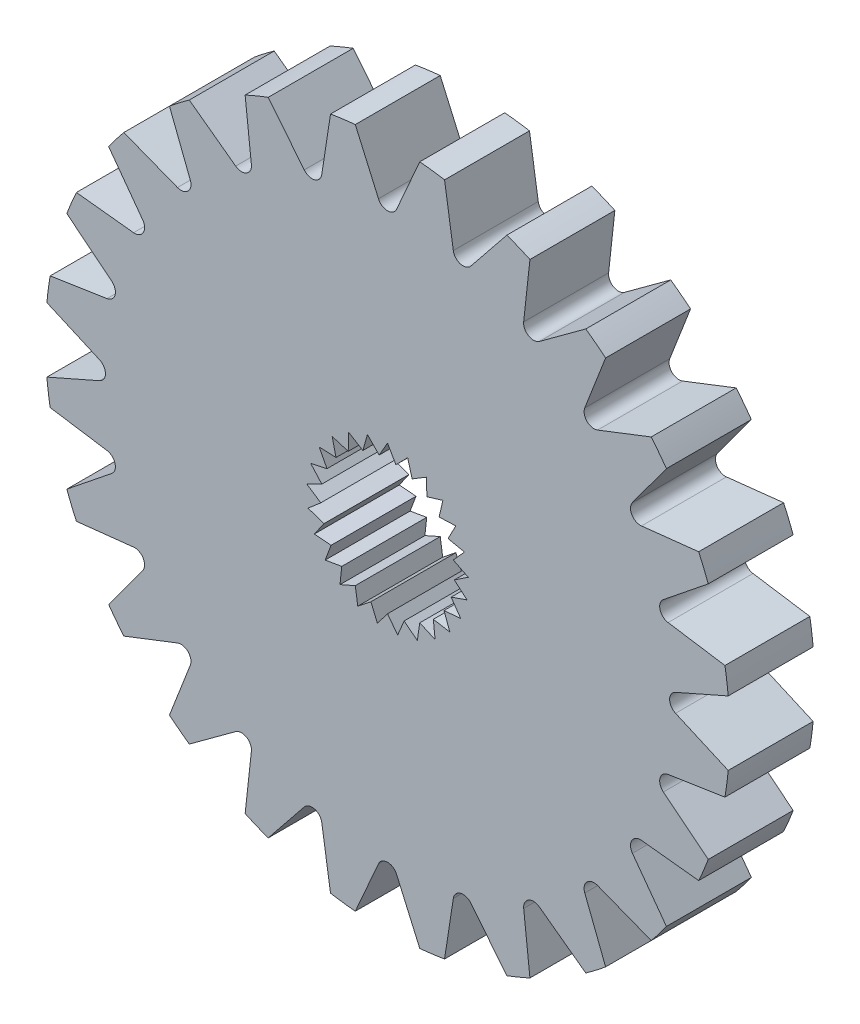
SolidWorks part; units mm, degrees
ref_plane "Front Plane" through (0, 0, 0) normal (0, 0, 1) x (1, 0, 0)
ref_plane "Top Plane" through (0, 0, 0) normal (0, 1, 0) x (1, 0, 0)
ref_plane "Right Plane" through (0, 0, 0) normal (1, 0, 0) x (0, 0, -1)
sketch "Sketch1" plane through (0, 0, 0) normal (0, 0, 1) x (1, 0, 0)
  line L0 (0, 3.048) -> (0, 0) construction
  line L1 (0, 3.048) -> (-0.3159, 2.5008)
  line L2 (0, 3.048) -> (0.3159, 2.5008)
  line L3 (-0.3159, 2.5008) -> (0.3159, 2.5008) construction
  line L4 (0.758, 2.9522) -> (0.3159, 2.5008)
  line L5 (0.758, 2.9522) -> (0.9279, 2.3437)
  line L6 (0.3159, 2.5008) -> (0.9279, 2.3437) construction
  line L7 (1.4684, 2.671) -> (0.9279, 2.3437)
  line L8 (1.4684, 2.671) -> (1.4816, 2.0393)
  line L9 (0.9279, 2.3437) -> (1.4816, 2.0393) construction
  line L10 (2.0865, 2.2219) -> (1.4816, 2.0393)
  line L11 (2.0865, 2.2219) -> (1.9422, 1.6067)
  line L12 (1.4816, 2.0393) -> (1.9422, 1.6067) construction
  line L13 (2.5735, 1.6332) -> (1.9422, 1.6067)
  line L14 (2.5735, 1.6332) -> (2.2808, 1.0733)
  line L15 (1.9422, 1.6067) -> (2.2808, 1.0733) construction
  line L16 (2.8988, 0.9419) -> (2.2808, 1.0733)
  line L17 (2.8988, 0.9419) -> (2.476, 0.4723)
  line L18 (2.2808, 1.0733) -> (2.476, 0.4723) construction
  line L19 (3.042, 0.1914) -> (2.476, 0.4723)
  line L20 (3.042, 0.1914) -> (2.5157, -0.1583)
  line L21 (2.476, 0.4723) -> (2.5157, -0.1583) construction
  line L22 (2.994, -0.5711) -> (2.5157, -0.1583)
  line L23 (2.994, -0.5711) -> (2.3973, -0.7789)
  line L24 (2.5157, -0.1583) -> (2.3973, -0.7789) construction
  line L25 (2.7579, -1.2978) -> (2.3973, -0.7789)
  line L26 (2.7579, -1.2978) -> (2.1283, -1.3506)
  line L27 (2.3973, -0.7789) -> (2.1283, -1.3506) construction
  line L28 (2.3485, -1.9429) -> (2.1283, -1.3506)
  line L29 (2.3485, -1.9429) -> (1.7255, -1.8375)
  line L30 (2.1283, -1.3506) -> (1.7255, -1.8375) construction
  line L31 (1.7916, -2.4659) -> (1.7255, -1.8375)
  line L32 (1.7916, -2.4659) -> (1.2143, -2.2089)
  line L33 (1.7255, -1.8375) -> (1.2143, -2.2089) construction
  line L34 (1.122, -2.834) -> (1.2143, -2.2089)
  line L35 (1.122, -2.834) -> (0.6269, -2.4415)
  line L36 (1.2143, -2.2089) -> (0.6269, -2.4415) construction
  line L37 (0.382, -3.024) -> (0.6269, -2.4415)
  line L38 (0.382, -3.024) -> (0, -2.5207)
  line L39 (0.6269, -2.4415) -> (0, -2.5207) construction
  line L40 (-0.382, -3.024) -> (0, -2.5207)
  line L41 (-0.382, -3.024) -> (-0.6269, -2.4415)
  line L42 (0, -2.5207) -> (-0.6269, -2.4415) construction
  line L43 (-1.122, -2.834) -> (-0.6269, -2.4415)
  line L44 (-1.122, -2.834) -> (-1.2143, -2.2089)
  line L45 (-0.6269, -2.4415) -> (-1.2143, -2.2089) construction
  line L46 (-1.7916, -2.4659) -> (-1.2143, -2.2089)
  line L47 (-1.7916, -2.4659) -> (-1.7255, -1.8375)
  line L48 (-1.2143, -2.2089) -> (-1.7255, -1.8375) construction
  line L49 (-2.3485, -1.9429) -> (-1.7255, -1.8375)
  line L50 (-2.3485, -1.9429) -> (-2.1283, -1.3506)
  line L51 (-1.7255, -1.8375) -> (-2.1283, -1.3506) construction
  line L52 (-2.7579, -1.2978) -> (-2.1283, -1.3506)
  line L53 (-2.7579, -1.2978) -> (-2.3973, -0.7789)
  line L54 (-2.1283, -1.3506) -> (-2.3973, -0.7789) construction
  line L55 (-2.994, -0.5711) -> (-2.3973, -0.7789)
  line L56 (-2.994, -0.5711) -> (-2.5157, -0.1583)
  line L57 (-2.3973, -0.7789) -> (-2.5157, -0.1583) construction
  line L58 (-3.042, 0.1914) -> (-2.5157, -0.1583)
  line L59 (-3.042, 0.1914) -> (-2.476, 0.4723)
  line L60 (-2.5157, -0.1583) -> (-2.476, 0.4723) construction
  line L61 (-2.8988, 0.9419) -> (-2.476, 0.4723)
  line L62 (-2.8988, 0.9419) -> (-2.2808, 1.0733)
  line L63 (-2.476, 0.4723) -> (-2.2808, 1.0733) construction
  line L64 (-2.5735, 1.6332) -> (-2.2808, 1.0733)
  line L65 (-2.5735, 1.6332) -> (-1.9422, 1.6067)
  line L66 (-2.2808, 1.0733) -> (-1.9422, 1.6067) construction
  line L67 (-2.0865, 2.2219) -> (-1.9422, 1.6067)
  line L68 (-2.0865, 2.2219) -> (-1.4816, 2.0393)
  line L69 (-1.9422, 1.6067) -> (-1.4816, 2.0393) construction
  line L70 (-1.4684, 2.671) -> (-1.4816, 2.0393)
  line L71 (-1.4684, 2.671) -> (-0.9279, 2.3437)
  line L72 (-1.4816, 2.0393) -> (-0.9279, 2.3437) construction
  line L73 (-0.758, 2.9522) -> (-0.9279, 2.3437)
  line L74 (-0.758, 2.9522) -> (-0.3159, 2.5008)
  line L75 (-0.9279, 2.3437) -> (-0.3159, 2.5008) construction
  circle A1 centre (0, 0) radius 12.8934
  point P0 (0, 2.5008)
  point P12 (0.6219, 2.4222)
  point P16 (1.2048, 2.1915)
  point P20 (1.7119, 1.823)
  point P24 (2.1115, 1.34)
  point P28 (2.3784, 0.7728)
  point P32 (2.4959, 0.157)
  point P36 (2.4565, -0.4686)
  point P40 (2.2628, -1.0648)
  point P44 (1.9269, -1.5941)
  point P48 (1.4699, -2.0232)
  point P52 (0.9206, -2.3252)
  point P56 (0.3134, -2.4811)
  point P60 (-0.3134, -2.4811)
  point P64 (-0.9206, -2.3252)
  point P68 (-1.4699, -2.0232)
  point P72 (-1.9269, -1.5941)
  point P76 (-2.2628, -1.0648)
  point P80 (-2.4565, -0.4686)
  point P84 (-2.4959, 0.157)
  point P88 (-2.3784, 0.7728)
  point P92 (-2.1115, 1.34)
  point P96 (-1.7119, 1.823)
  point P100 (-1.2048, 2.1915)
  point P104 (-0.6219, 2.4222)
  dimension "D1" = 25
  dimension "D3" = 25.7868
  dimension "D2" = 60
extrude "Boss-Extrude1" add sketch "Sketch1" along normal blind 3.2004
sketch "Sketch2" plane through (0, 0, 3.2004) normal (0, 0, 1) x (1, 0, 0)
  line L0 (-1.2151, 12.836) -> (1.2151, 12.836) construction
  line L1 (-1.2151, 12.836) -> (-0.3419, 10.8524)
  line L2 (0, 0) -> (0.8437, 12.836) construction
  line L3 (0.3419, 10.8524) -> (1.2151, 12.836)
  line L4 (-0.3419, 10.8524) -> (0.3419, 10.8524) construction
  line L5 (3.1391, 10.3941) -> (4.4959, 12.0841)
  line L6 (-0.7785, 11.8442) -> (0.7785, 11.8442) construction
  line L7 (2.1485, 12.7131) -> (2.4786, 10.5711)
  line L8 (5.7223, 9.2275) -> (7.4703, 10.5087)
  line L9 (5.3657, 11.7239) -> (5.1301, 9.5694)
  line L10 (7.9156, 7.4321) -> (9.9357, 8.2172)
  line L11 (8.2172, 9.9357) -> (7.4321, 7.9156)
  line L12 (9.5694, 5.1301) -> (11.7239, 5.3657)
  line L13 (10.5087, 7.4703) -> (9.2275, 5.7223)
  line L14 (10.5711, 2.4786) -> (12.7131, 2.1485)
  line L15 (12.0841, 4.4959) -> (10.3941, 3.1391)
  line L16 (10.8524, -0.3419) -> (12.836, -1.2151)
  line L17 (12.836, 1.2151) -> (10.8524, 0.3419)
  line L18 (10.3941, -3.1391) -> (12.0841, -4.4959)
  line L19 (12.7131, -2.1485) -> (10.5711, -2.4786)
  line L20 (9.2275, -5.7223) -> (10.5087, -7.4703)
  line L21 (11.7239, -5.3657) -> (9.5694, -5.1301)
  line L22 (7.4321, -7.9156) -> (8.2172, -9.9357)
  line L23 (9.9357, -8.2172) -> (7.9156, -7.4321)
  line L24 (5.1301, -9.5694) -> (5.3657, -11.7239)
  line L25 (7.4703, -10.5087) -> (5.7223, -9.2275)
  line L26 (2.4786, -10.5711) -> (2.1485, -12.7131)
  line L27 (4.4959, -12.0841) -> (3.1391, -10.3941)
  line L28 (-0.3419, -10.8524) -> (-1.2151, -12.836)
  line L29 (1.2151, -12.836) -> (0.3419, -10.8524)
  line L30 (-3.1391, -10.3941) -> (-4.4959, -12.0841)
  line L31 (-2.1485, -12.7131) -> (-2.4786, -10.5711)
  line L32 (-5.7223, -9.2275) -> (-7.4703, -10.5087)
  line L33 (-5.3657, -11.7239) -> (-5.1301, -9.5694)
  line L34 (-7.9156, -7.4321) -> (-9.9357, -8.2172)
  line L35 (-8.2172, -9.9357) -> (-7.4321, -7.9156)
  line L36 (-9.5694, -5.1301) -> (-11.7239, -5.3657)
  line L37 (-10.5087, -7.4703) -> (-9.2275, -5.7223)
  line L38 (-10.5711, -2.4786) -> (-12.7131, -2.1485)
  line L39 (-12.0841, -4.4959) -> (-10.3941, -3.1391)
  line L40 (-10.8524, 0.3419) -> (-12.836, 1.2151)
  line L41 (-12.836, -1.2151) -> (-10.8524, -0.3419)
  line L42 (-10.3941, 3.1391) -> (-12.0841, 4.4959)
  line L43 (-12.7131, 2.1485) -> (-10.5711, 2.4786)
  line L44 (-9.2275, 5.7223) -> (-10.5087, 7.4703)
  line L45 (-11.7239, 5.3657) -> (-9.5694, 5.1301)
  line L46 (-7.4321, 7.9156) -> (-8.2172, 9.9357)
  line L47 (-9.9357, 8.2172) -> (-7.9156, 7.4321)
  line L48 (-5.1301, 9.5694) -> (-5.3657, 11.7239)
  line L49 (-7.4703, 10.5087) -> (-5.7223, 9.2275)
  line L50 (-2.4786, 10.5711) -> (-2.1485, 12.7131)
  line L51 (-4.4959, 12.0841) -> (-3.1391, 10.3941)
  line L180 (0, 12.836) -> (0, 0) construction
  arc A0 (0.3419, 10.8524) -> (-0.3419, 10.8524) centre (0, 11.0029) cw
  arc A1 (1.2151, 12.836) -> (-1.2151, 12.836) centre (0, 0) ccw
  arc A2 (4.4959, 12.0841) -> (2.1485, 12.7131) centre (0, 0) ccw
  circle A3 centre (0, 0) radius 12.8934 construction
  arc A4 (3.1391, 10.3941) -> (2.4786, 10.5711) centre (2.8478, 10.628) cw
  arc A5 (7.4703, 10.5087) -> (5.3657, 11.7239) centre (0, 0) ccw
  arc A6 (5.7223, 9.2275) -> (5.1301, 9.5694) centre (5.5015, 9.5288) cw
  arc A7 (9.9357, 8.2172) -> (8.2172, 9.9357) centre (0, 0) ccw
  arc A8 (7.9156, 7.4321) -> (7.4321, 7.9156) centre (7.7802, 7.7802) cw
  arc A9 (11.7239, 5.3657) -> (10.5087, 7.4703) centre (0, 0) ccw
  arc A10 (9.5694, 5.1301) -> (9.2275, 5.7223) centre (9.5288, 5.5015) cw
  arc A11 (12.7131, 2.1485) -> (12.0841, 4.4959) centre (0, 0) ccw
  arc A12 (10.5711, 2.4786) -> (10.3941, 3.1391) centre (10.628, 2.8478) cw
  arc A13 (12.836, -1.2151) -> (12.836, 1.2151) centre (0, 0) ccw
  arc A14 (10.8524, -0.3419) -> (10.8524, 0.3419) centre (11.0029, 0) cw
  arc A15 (12.0841, -4.4959) -> (12.7131, -2.1485) centre (0, 0) ccw
  arc A16 (10.3941, -3.1391) -> (10.5711, -2.4786) centre (10.628, -2.8478) cw
  arc A17 (10.5087, -7.4703) -> (11.7239, -5.3657) centre (0, 0) ccw
  arc A18 (9.2275, -5.7223) -> (9.5694, -5.1301) centre (9.5288, -5.5015) cw
  arc A19 (8.2172, -9.9357) -> (9.9357, -8.2172) centre (0, 0) ccw
  arc A20 (7.4321, -7.9156) -> (7.9156, -7.4321) centre (7.7802, -7.7802) cw
  arc A21 (5.3657, -11.7239) -> (7.4703, -10.5087) centre (0, 0) ccw
  arc A22 (5.1301, -9.5694) -> (5.7223, -9.2275) centre (5.5015, -9.5288) cw
  arc A23 (2.1485, -12.7131) -> (4.4959, -12.0841) centre (0, 0) ccw
  arc A24 (2.4786, -10.5711) -> (3.1391, -10.3941) centre (2.8478, -10.628) cw
  arc A25 (-1.2151, -12.836) -> (1.2151, -12.836) centre (0, 0) ccw
  arc A26 (-0.3419, -10.8524) -> (0.3419, -10.8524) centre (0, -11.0029) cw
  arc A27 (-4.4959, -12.0841) -> (-2.1485, -12.7131) centre (0, 0) ccw
  arc A28 (-3.1391, -10.3941) -> (-2.4786, -10.5711) centre (-2.8478, -10.628) cw
  arc A29 (-7.4703, -10.5087) -> (-5.3657, -11.7239) centre (0, 0) ccw
  arc A30 (-5.7223, -9.2275) -> (-5.1301, -9.5694) centre (-5.5015, -9.5288) cw
  arc A31 (-9.9357, -8.2172) -> (-8.2172, -9.9357) centre (0, 0) ccw
  arc A32 (-7.9156, -7.4321) -> (-7.4321, -7.9156) centre (-7.7802, -7.7802) cw
  arc A33 (-11.7239, -5.3657) -> (-10.5087, -7.4703) centre (0, 0) ccw
  arc A34 (-9.5694, -5.1301) -> (-9.2275, -5.7223) centre (-9.5288, -5.5015) cw
  arc A35 (-12.7131, -2.1485) -> (-12.0841, -4.4959) centre (0, 0) ccw
  arc A36 (-10.5711, -2.4786) -> (-10.3941, -3.1391) centre (-10.628, -2.8478) cw
  arc A37 (-12.836, 1.2151) -> (-12.836, -1.2151) centre (0, 0) ccw
  arc A38 (-10.8524, 0.3419) -> (-10.8524, -0.3419) centre (-11.0029, 0) cw
  arc A39 (-12.0841, 4.4959) -> (-12.7131, 2.1485) centre (0, 0) ccw
  arc A40 (-10.3941, 3.1391) -> (-10.5711, 2.4786) centre (-10.628, 2.8478) cw
  arc A41 (-10.5087, 7.4703) -> (-11.7239, 5.3657) centre (0, 0) ccw
  arc A42 (-9.2275, 5.7223) -> (-9.5694, 5.1301) centre (-9.5288, 5.5015) cw
  arc A43 (-8.2172, 9.9357) -> (-9.9357, 8.2172) centre (0, 0) ccw
  arc A44 (-7.4321, 7.9156) -> (-7.9156, 7.4321) centre (-7.7802, 7.7802) cw
  arc A45 (-5.3657, 11.7239) -> (-7.4703, 10.5087) centre (0, 0) ccw
  arc A46 (-5.1301, 9.5694) -> (-5.7223, 9.2275) centre (-5.5015, 9.5288) cw
  arc A47 (-2.1485, 12.7131) -> (-4.4959, 12.0841) centre (0, 0) ccw
  arc A48 (-2.4786, 10.5711) -> (-3.1391, 10.3941) centre (-2.8478, 10.628) cw
  point P1 (0, 11.8442)
  point P132 (0, 0)
  point P212 (0, 0)
  dimension "D1" = 0.9918
  dimension "D2" = 20
  dimension "D3" = 24
  dimension "D5" = 1.557
extrude "Cut-Extrude1" cut sketch "Sketch2" against normal up to surface (3.2004 mm away) up to face at (12.8934, 0, 0)
sketch "Sketch3" plane through (0, 0, 3.2004) normal (0, 0, 1) x (1, 0, 0)
  circle A0 centre (0, 0) radius 11.9016 construction
  circle A1 centre (0, 0) radius 12.8934 construction
  dimension "D1" = 23.8032
